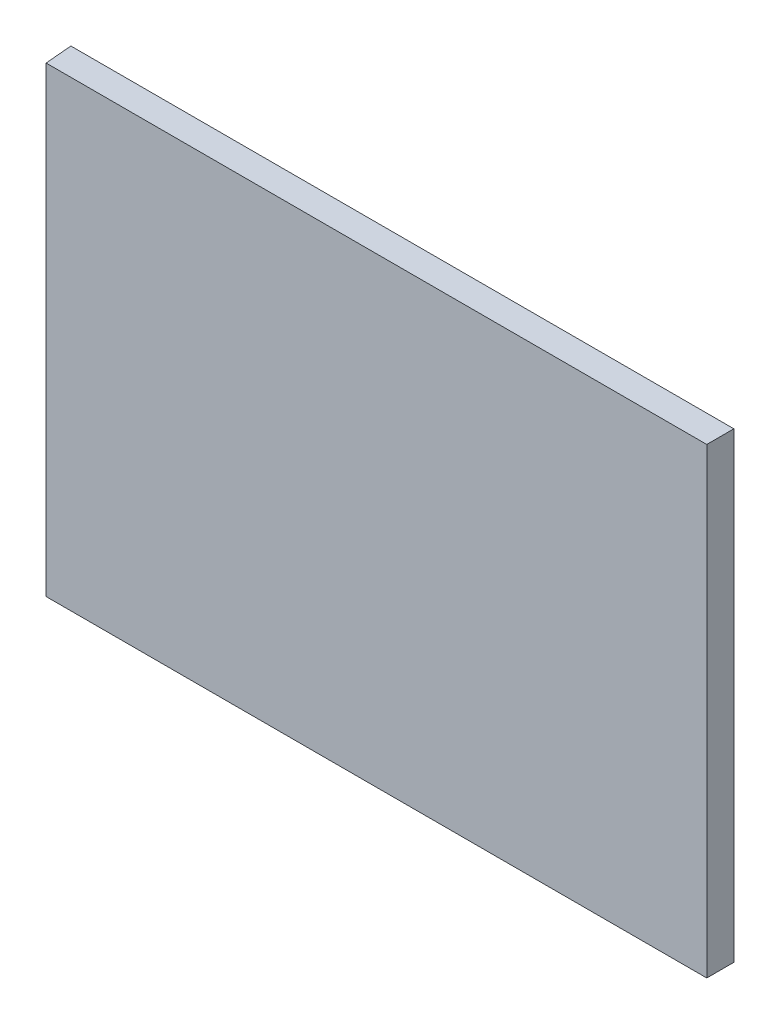
SolidWorks part; units mm, degrees
ref_plane "前视基准面" through (0, 0, 0) normal (0, 0, 1) x (1, 0, 0)
ref_plane "上视基准面" through (0, 0, 0) normal (0, 1, 0) x (1, 0, 0)
ref_plane "右视基准面" through (0, 0, 0) normal (1, 0, 0) x (0, 0, -1)
other "Configuration Table"
sketch "草图4" plane through (0, 0, 0) normal (0, 0, 1) x (1, 0, 0)
  line L0 (-11.0381, 9) -> (14.9119, 9)
  line L1 (-11.0381, 9) -> (-11.0381, -12.04)
  line L2 (-11.0381, -12.04) -> (14.9119, -12.04)
  line L3 (14.9119, 9) -> (14.9119, -12.04)
  dimension "D1" = 21.04
  dimension "D2" = 25.95
extrude "凸台-拉伸1" add sketch "草图4" along normal blind 1
sketch "草图6" plane through (0, 9, 0) normal (0, 1, 0) x (1, 0, 0)
  line L0 (-11.0381, 0) -> (-11.0381, -1)
  line L1 (-11.0381, -1) -> (-10.9506, -1)
  line L2 (14.9119, -1) -> (-11.0381, -1) construction
  line L3 (-10.9506, -1) -> (-11.0381, 0)
  dimension "D1" = 5
extrude "切除-拉伸1" cut sketch "草图6" against normal through all
sketch "草图7" plane through (0, 9, 0) normal (0, 1, 0) x (1, 0, 0)
  line L0 (14.9119, -1) -> (14.8944, 0)
  line L1 (14.9119, 0) -> (-11.0381, 0) construction
  line L2 (14.8944, 0) -> (14.9119, 0)
  line L3 (14.9119, 0) -> (14.9119, -1)
  dimension "D1" = 1
extrude "切除-拉伸2" cut sketch "草图7" against normal through all
sketch "草图11" plane through (0, 0, 0) normal (1, 0, 0) x (0, 0, -1)
  line L0 (-1, -12.04) -> (0, -12.04)
  line L1 (0, -12.04) -> (0, -12.0225)
  line L2 (0, -12.04) -> (0, 9) construction
  line L3 (0, -12.0225) -> (-1, -12.04)
  dimension "D1" = 1
extrude "切除-拉伸4" cut sketch "草图11" against normal through all and the other way through all
sketch "草图12" plane through (0, 0, 0) normal (1, 0, 0) x (0, 0, -1)
  line L3 (-1, 9) -> (0, 9)
  line L4 (-1, 9) -> (0, 8.9825)
  line L5 (0, -12.0225) -> (0, 9) construction
  line L6 (0, 8.9825) -> (0, 9)
  dimension "D1" = 1
extrude "切除-拉伸5" cut sketch "草图12" against normal through all and the other way through all
sketch "草图13" plane through (0, 0, 1) normal (0, 0, 1) x (1, 0, 0)
  line L0 (-10.9506, 7) -> (13.4119, 7)
  line L1 (-10.9506, -12.04) -> (-10.9506, 9) construction
  line L2 (13.4119, 7) -> (13.4119, -10.04)
  line L3 (13.4119, -10.04) -> (-10.9506, -10.04)
  line L4 (-10.9506, -10.04) -> (-10.9506, -12.04)
  line L5 (-10.9506, -12.04) -> (14.9119, -12.04)
  line L6 (14.9119, -12.04) -> (14.9119, 9)
  line L7 (14.9119, 9) -> (-10.9506, 9)
  line L8 (-10.9506, 9) -> (-10.9506, 7)
  dimension "D1" = 2
  dimension "D2" = 2
  dimension "D3" = 1.5
extrude "切除-拉伸6" cut sketch "草图13" against normal up to surface (1 mm away) up to face at (1.9281, -1.52, 0)
sketch "草图14" plane through (-10.9506, 0, 0) normal (1, 0, 0) x (0, 0, -1)
  line L1 (-1, 9) -> (0, 9)
  line L2 (-1, 9) -> (-1, 7)
  line L3 (-1, 7) -> (0, 7)
  line L4 (0, 9) -> (0, 7)
  line L5 (-1, -10.04) -> (0, -10.04)
  line L6 (-1, -10.04) -> (-1, -12.04)
  line L7 (-1, -12.04) -> (0, -12.04)
  line L8 (0, -10.04) -> (0, -12.04)
  point P12 (-1, -12.0225)
  point P13 (-1, -12.04)
extrude "切除-拉伸7" cut sketch "草图14" against normal blind 10
